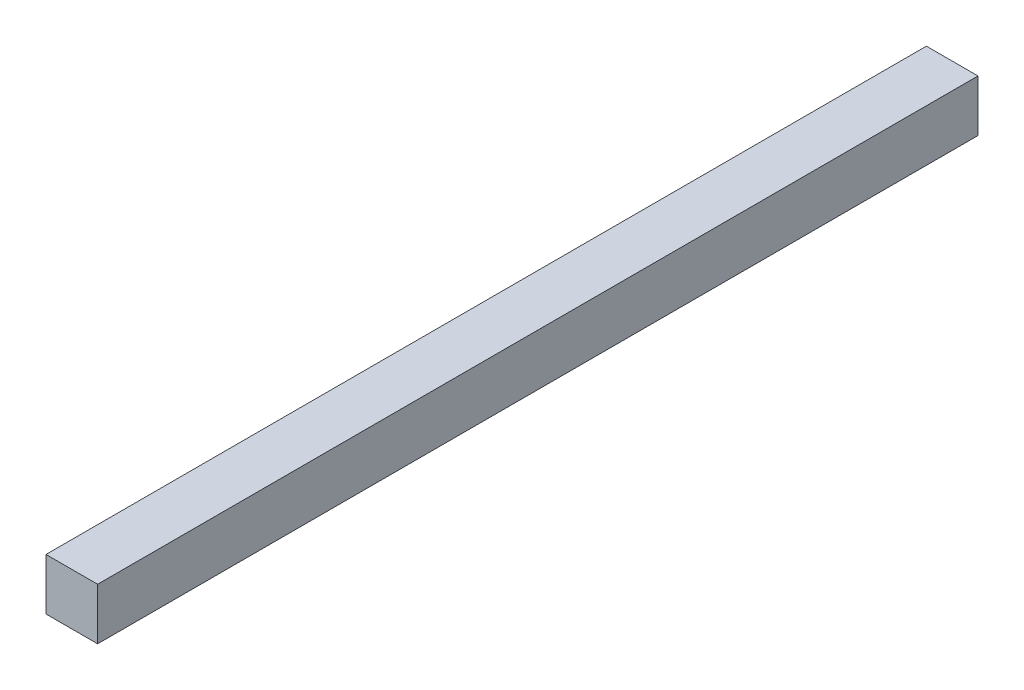
SolidWorks part; units mm, degrees
material "Plain Carbon Steel"
ref_plane "Front Plane" through (0, 0, 0) normal (0, 0, 1) x (1, 0, 0)
ref_plane "Top Plane" through (0, 0, 0) normal (0, 1, 0) x (1, 0, 0)
ref_plane "Right Plane" through (0, 0, 0) normal (1, 0, 0) x (0, 0, -1)
sketch "Sketch1" plane through (0, 0, 0) normal (0, 0, 1) x (1, 0, 0)
  line L1 (0, 0) -> (35, 0)
  line L2 (0, 0) -> (0, 35)
  line L3 (0, 35) -> (35, 35)
  line L4 (35, 0) -> (35, 35)
  dimension "D1" = 35
  dimension "D2" = 35
extrude "Boss-Extrude1" add sketch "Sketch1" along normal blind 597 contours L2 L3 L4 L1
